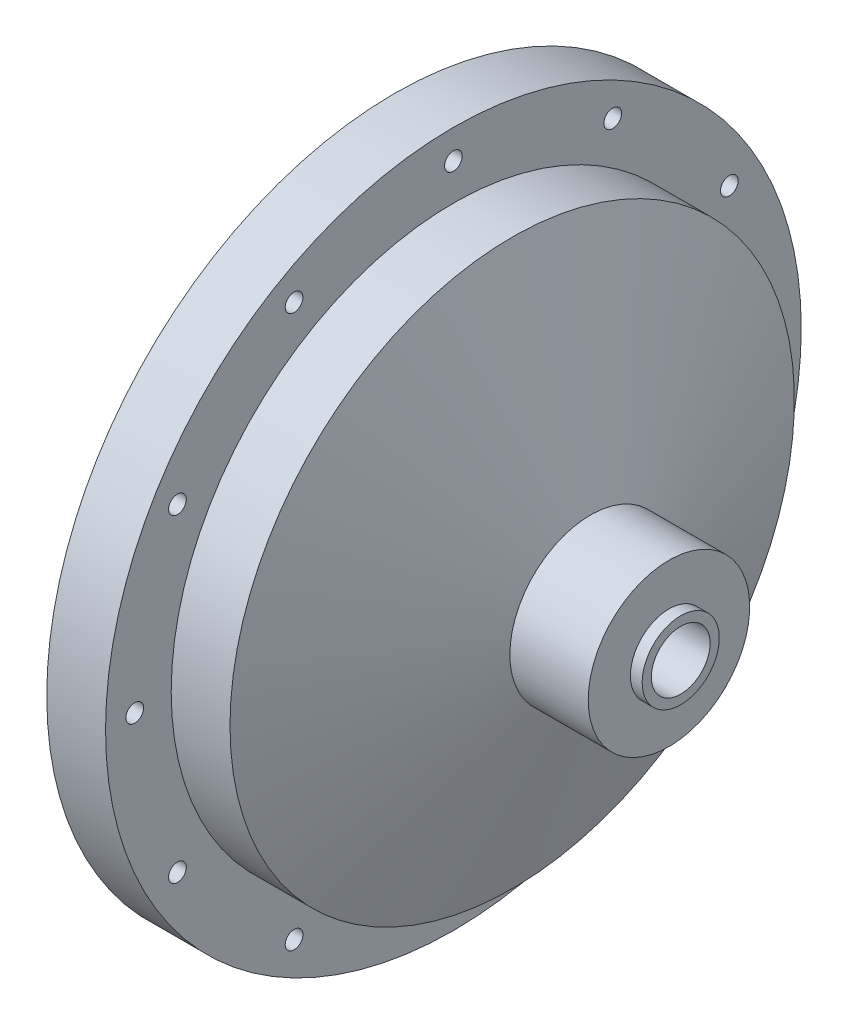
SolidWorks part; units mm, degrees
material "7075-T6 (SN)"
ref_plane "Front Plane" through (0, 0, 0) normal (0, 0, 1) x (1, 0, 0)
ref_plane "Top Plane" through (0, 0, 0) normal (0, 1, 0) x (1, 0, 0)
ref_plane "Right Plane" through (0, 0, 0) normal (1, 0, 0) x (0, 0, -1)
sketch "Sketch2" plane through (0, 0, 0) normal (0, 0, 1) x (1, 0, 0)
  line L0 (0, 0) -> (165.0115, 0) construction
  line L1 (0, 0) -> (0, 56.3562)
  line L2 (0, 56.3562) -> (9.525, 56.3562)
  line L4 (19.05, 45.72) -> (31.75, 13.081)
  line L5 (44.45, 13.081) -> (44.45, 6.2484)
  line L6 (31.75, 13.081) -> (44.45, 13.081)
  line L7 (44.45, 6.2484) -> (46.355, 6.2484)
  line L8 (46.355, 6.2484) -> (46.355, 0)
  line L9 (0, 0) -> (46.355, 0)
  line L11 (19.05, 45.72) -> (9.525, 45.72)
  line L14 (9.525, 45.72) -> (9.525, 56.3562)
  dimension "D1" = 56.3562
  dimension "D2" = 9.525
  dimension "D3" = 45.72
  dimension "D4" = 13.081
  dimension "D5" = 12.7
  dimension "D6" = 12.7
  dimension "D7" = 6.2484
  dimension "D8" = 1.905
  dimension "D9" = 9.525
revolve "Main Structure" add sketch "Sketch2" angle 360 about L0
cosmetic thread "Cosmetic Thread1" parameters "D2"=23.1953
sketch "Sketch3" plane through (46.355, 0, 0) normal (1, 0, 0) x (0, 0, -1)
  circle A0 centre (0, 0) radius 4.7625
  dimension "D1" = 9.525
extrude "Oxidizer Inlet Hole" cut sketch "Sketch3" against normal through all
sketch "Sketch4" plane through (0, 0, 0) normal (-1, 0, 0) x (0, 0, 1)
  circle A0 centre (0, 0) radius 51.6255 construction
  circle A1 centre (0, -51.6255) radius 2.146
  circle A2 centre (-25.8127, -44.709) radius 2.146
  circle A3 centre (-44.709, -25.8128) radius 2.146
  circle A4 centre (-51.6255, 0) radius 2.146
  circle A5 centre (-44.709, 25.8127) radius 2.146
  circle A6 centre (-25.8128, 44.709) radius 2.146
  circle A7 centre (0, 51.6255) radius 2.146
  circle A8 centre (25.8127, 44.709) radius 2.146
  circle A9 centre (44.709, 25.8128) radius 2.146
  circle A10 centre (51.6255, 0) radius 2.146
  circle A11 centre (44.709, -25.8127) radius 2.146
  circle A12 centre (25.8128, -44.709) radius 2.146
  point P29 (0, 0)
  dimension "D1" = 12
  dimension "D2" = 103.251
hole_wizard "Flange Holes" positions "Sketch7" profile "Sketch8" hole size "#33" standard "ANSI Inch" end condition up to next
sketch "Sketch7" plane through (0, 0, 0) normal (-1, 0, 0) x (0, 0, 1)
  point P0 (0, -51.6255)
  point P3 (-25.8127, -44.709)
  point P6 (-44.709, -25.8128)
  point P9 (-51.6255, 0)
  point P12 (-44.709, 25.8127)
  point P15 (-25.8128, 44.709)
  point P18 (0, 51.6255)
  point P21 (25.8127, 44.709)
  point P24 (44.709, 25.8128)
  point P27 (51.6255, 0)
  point P30 (44.709, -25.8127)
  point P33 (25.8128, -44.709)
sketch "Sketch8" plane through (0, -51.6255, 0) normal (0, 1, 0) x (0, 0, 1)
  line L0 (0, 0) -> (0, 9.525)
  line L1 (0, 9.525) -> (1.4351, 9.525)
  line L2 (1.4351, 9.525) -> (1.4351, 0)
  line L5 (1.4351, 0) -> (0, 0)
  line L11 (0, -6.35) -> (0, 107.95) construction
  dimension "Thru Hole Dia." = 2.8702
  dimension "Thru Hole Depth" = 9.525
sketch "Sketch9" plane through (0, 0, 0) normal (-1, 0, 0) x (0, 0, 1)
  line L0 (0, 0) -> (-67.6727, 18.1329) construction
  line L1 (0, 0) -> (-51.6255, 0) construction
  circle A0 centre (0, 0) radius 51.6255 construction
  circle A1 centre (-49.8664, 13.3617) radius 2.9451
  circle A2 centre (49.8664, -13.3617) radius 2.9451
  point P14 (0, 0)
  dimension "D1" = 15
  dimension "D2" = 2
hole_wizard "Dowel Holes" positions "Sketch10" profile "Sketch11" hole size "3/16" standard "ANSI Inch"
sketch "Sketch10" plane through (0, 0, 0) normal (-1, 0, 0) x (0, 0, 1)
  point P0 (49.8664, -13.3617)
  point P3 (-49.8664, 13.3617)
sketch "Sketch11" plane through (0, -13.3617, 49.8664) normal (0, 1, 0) x (0, 0, 1)
  line L0 (0, 0) -> (0, 7.7808)
  line L1 (0, 7.7808) -> (2.3812, 6.35)
  line L2 (2.3812, 6.35) -> (2.3812, 0)
  line L5 (2.3812, 0) -> (0, 0)
  line L10 (0, 7.7808) -> (-2.3812, 6.35) construction
  line L11 (0, -6.35) -> (0, 107.95) construction
  dimension "Hole Dia." = 4.7625
  dimension "Hole Depth" = 6.35
  dimension "Drill Angle" = 118
sketch "Sketch12" plane through (0, 0, 0) normal (-1, 0, 0) x (0, 0, 1)
  circle A0 centre (0, 0) radius 38.1
  dimension "D1" = 76.2
extrude "Impinging Plate Flat Cut" cut sketch "Sketch12" against normal blind 3.81
ref_plane "Plane1" through (6.35, 0, 0) normal (-1, 0, 0) x (0, 0, 1)
sketch "Sketch14" plane through (3.81, 0, 0) normal (-1, 0, 0) x (0, 0, 1)
  circle A0 centre (0, 0) radius 38.1
  dimension "D1" = 76.2
sketch "Sketch15" plane through (6.35, 0, 0) normal (-1, 0, 0) x (0, 0, 1)
  circle A0 centre (0, 0) radius 38.1
  dimension "D1" = 76.2
ref_plane "Plane4" through (15.875, 0, 0) normal (-1, 0, 0) x (0, 0, 1)
loft "Impinging Plate Taper Cut" cut profiles "Sketch14", "Sketch15"
sketch "Sketch16" plane through (15.875, 0, 0) normal (-1, 0, 0) x (0, 0, 1)
  circle A0 centre (0, 0) radius 28.575
  dimension "D1" = 57.15
ref_plane "Plane2" through (31.115, 0, 0) normal (-1, 0, 0) x (0, 0, 1)
sketch "Sketch17" plane through (31.115, 0, 0) normal (-1, 0, 0) x (0, 0, 1)
  circle A0 centre (0, 0) radius 4.7625
  dimension "D1" = 9.525
loft "Internal Flow Path Loft Cut" cut profiles "Sketch16", "Sketch17"
sketch "Sketch21" plane through (6.35, 0, 0) normal (-1, 0, 0) x (0, 0, 1)
  circle A0 centre (0, 0) radius 28.575
  dimension "D1" = 57.15
extrude "Cut-Extrude1" cut sketch "Sketch21" against normal blind 9.525
fillet "Internal Fillet" radius 3.175 1 edges at (31.115, 0, 4.7625)
sketch "Sketch18" plane through (6.35, 0, 0) normal (-1, 0, 0) x (0, 0, 1)
  circle A0 centre (0, 0) radius 33.3375
  circle A1 centre (33.3375, 0) radius 1.5042
  dimension "D1" = 66.675
hole_wizard "4-40 Tapped Holes " positions "Sketch19" profile "Sketch20" hole size "#4-40" standard "ANSI Inch"
sketch "Sketch19" plane through (6.35, 0, 0) normal (-1, 0, 0) x (0, 0, 1)
  point P0 (33.3375, 0)
sketch "Sketch20" plane through (6.35, 0, 33.3375) normal (0, 1, 0) x (0, 0, 1)
  line L0 (0, 0) -> (0, 3.8542)
  line L1 (0, 3.8542) -> (1.1303, 3.175)
  line L2 (1.1303, 3.175) -> (1.1303, 0)
  line L5 (1.1303, 0) -> (0, 0)
  line L10 (0, 3.8542) -> (-1.1303, 3.175) construction
  line L11 (0, -6.35) -> (0, 107.95) construction
  dimension "Hole Dia." = 2.2606
  dimension "Hole Depth" = 3.175
  dimension "Drill Angle" = 118
pattern_circular "Extended 8 BC" count 8 over 360 about axis through (0, 0, 0) along (1, 0, 0) of "4-40 Tapped Holes "
chamfer "Chamfer for Impinging Edge" distance 0.127 angle 45 1 edges at (6.35, 0, 38.1)
